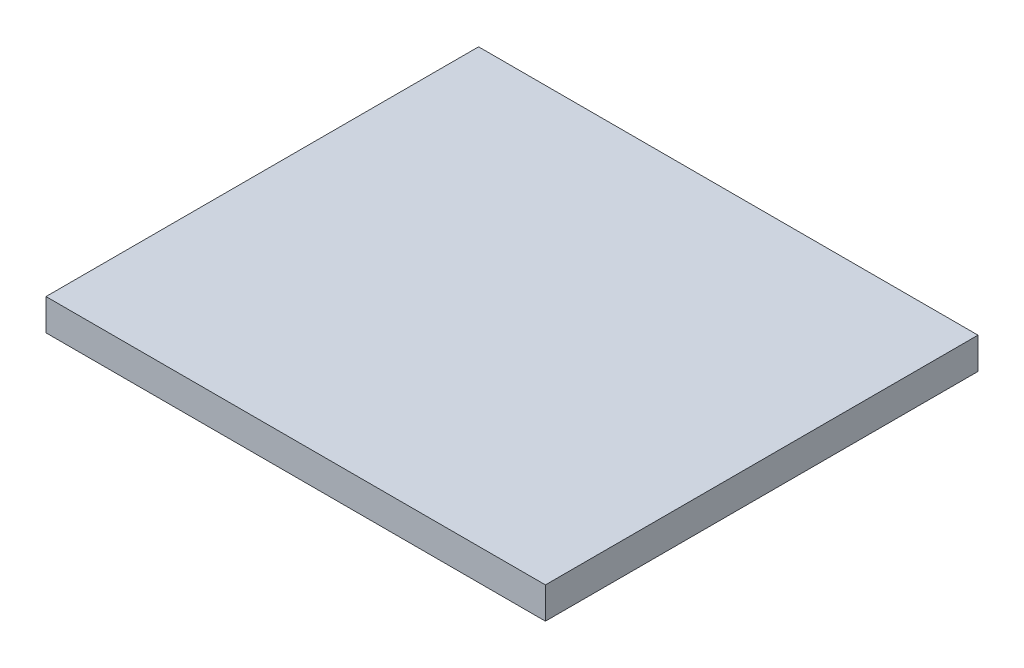
SolidWorks part; units mm, degrees
ref_plane "Alzado" through (0, 0, 0) normal (0, 0, 1) x (1, 0, 0)
ref_plane "Planta" through (0, 0, 0) normal (0, 1, 0) x (1, 0, 0)
ref_plane "Vista lateral" through (0, 0, 0) normal (1, 0, 0) x (0, 0, -1)
sketch "Croquis1" plane through (0, 0, 0) normal (0, 0, 1) x (1, 0, 0)
  line L5 (0, 0) -> (101.6, 0)
  line L6 (0, 0) -> (0, 6.4)
  line L7 (0, 6.4) -> (101.6, 6.4)
  line L8 (101.6, 0) -> (101.6, 6.4)
extrude "Saliente-Extruir2" add sketch "Croquis1" along normal blind 88
